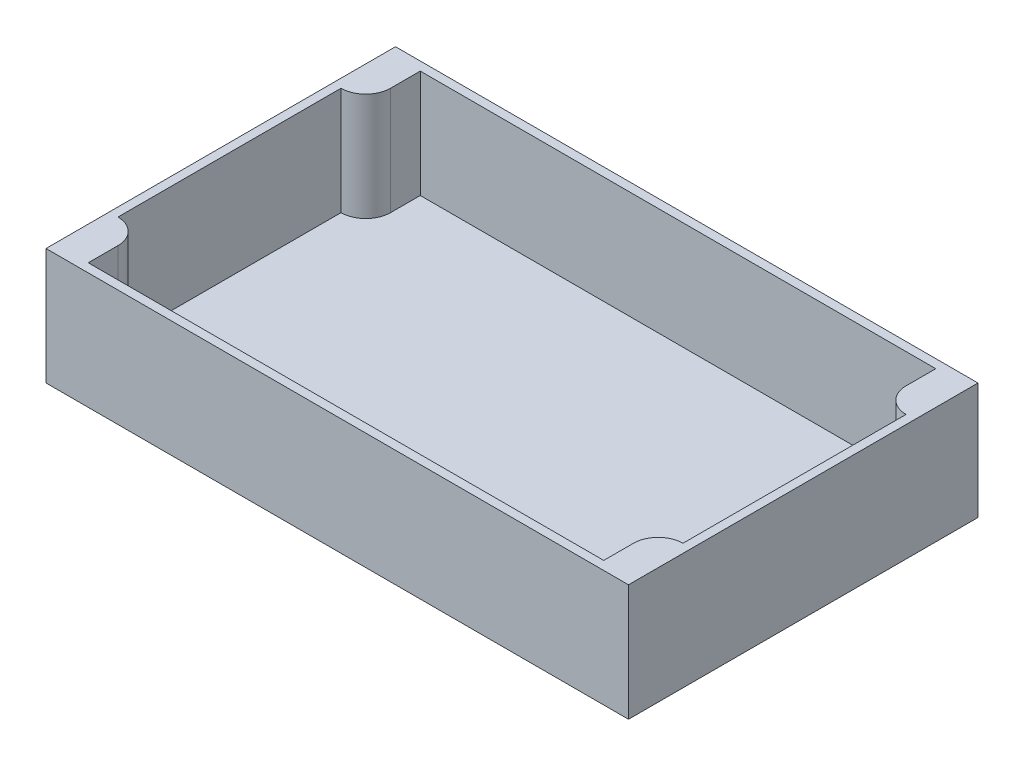
SolidWorks part; units mm, degrees
ref_plane "Front Plane" through (0, 0, 0) normal (0, 0, 1) x (1, 0, 0)
ref_plane "Top Plane" through (0, 0, 0) normal (0, 1, 0) x (1, 0, 0)
ref_plane "Right Plane" through (0, 0, 0) normal (1, 0, 0) x (0, 0, -1)
sketch "Sketch1" plane through (0, 0, 0) normal (0, 1, 0) x (1, 0, 0)
  line L1 (0, 0) -> (200, 0)
  line L2 (0, 0) -> (0, 120)
  line L3 (0, 120) -> (200, 120)
  line L4 (200, 0) -> (200, 120)
  dimension "D1" = 120
  dimension "D2" = 200
extrude "Boss-Extrude1" add sketch "Sketch1" along normal blind 3
sketch "Sketch2" plane through (0, 3, 0) normal (0, 1, 0) x (1, 0, 0)
  line L9 (0, 0) -> (0, 120)
  line L10 (0, 60) -> (3, 60) construction
  line L11 (3, 98.3) -> (3, 21.7)
  line L12 (11.5, 13.2) -> (11.5, 3)
  line L13 (0, 120) -> (0, 0) construction
  line L14 (0, 0) -> (200, 0) construction
  line L18 (11.5, 3) -> (188.5, 3)
  line L19 (100, 3) -> (100, 0) construction
  line L24 (200, 0) -> (0, 0)
  line L25 (100, 117) -> (100, 120) construction
  line L26 (200, 120) -> (0, 120)
  line L27 (11.5, 117) -> (188.5, 117)
  line L28 (11.5, 106.8) -> (11.5, 117)
  line L29 (200, 60) -> (197, 60) construction
  line L30 (188.5, 106.8) -> (188.5, 117)
  line L31 (188.5, 13.2) -> (188.5, 3)
  line L32 (197, 98.3) -> (197, 21.7)
  line L33 (200, 0) -> (200, 120)
  arc A4 (3, 21.7) -> (11.5, 13.2) centre (3, 13.2) cw
  arc A5 (3, 98.3) -> (11.5, 106.8) centre (3, 106.8) ccw
  arc A6 (197, 98.3) -> (188.5, 106.8) centre (197, 106.8) cw
  arc A7 (197, 21.7) -> (188.5, 13.2) centre (197, 13.2) ccw
  point P21 (0, 60)
  point P24 (100, 0)
  dimension "D1" = 3
  dimension "D2" = 88.5
  dimension "D3" = 38.3
extrude "Boss-Extrude2" add sketch "Sketch2" along direction (0, -1, 0) on the side of the normal offset from surface (37 mm away) 40
